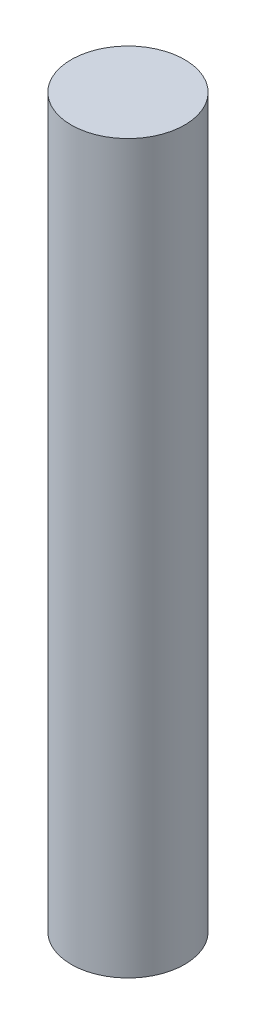
SolidWorks part; units mm, degrees
ref_plane "Front Plane" through (0, 0, 0) normal (0, 0, 1) x (1, 0, 0)
ref_plane "Top Plane" through (0, 0, 0) normal (0, 1, 0) x (1, 0, 0)
ref_plane "Right Plane" through (0, 0, 0) normal (1, 0, 0) x (0, 0, -1)
sketch "Sketch1" plane through (0, 0, 0) normal (0, 1, 0) x (1, 0, 0)
  circle A0 centre (0, 0) radius 3.9
  dimension "D1" = 7.8
extrude "Boss-Extrude1" add sketch "Sketch1" along normal blind 50
